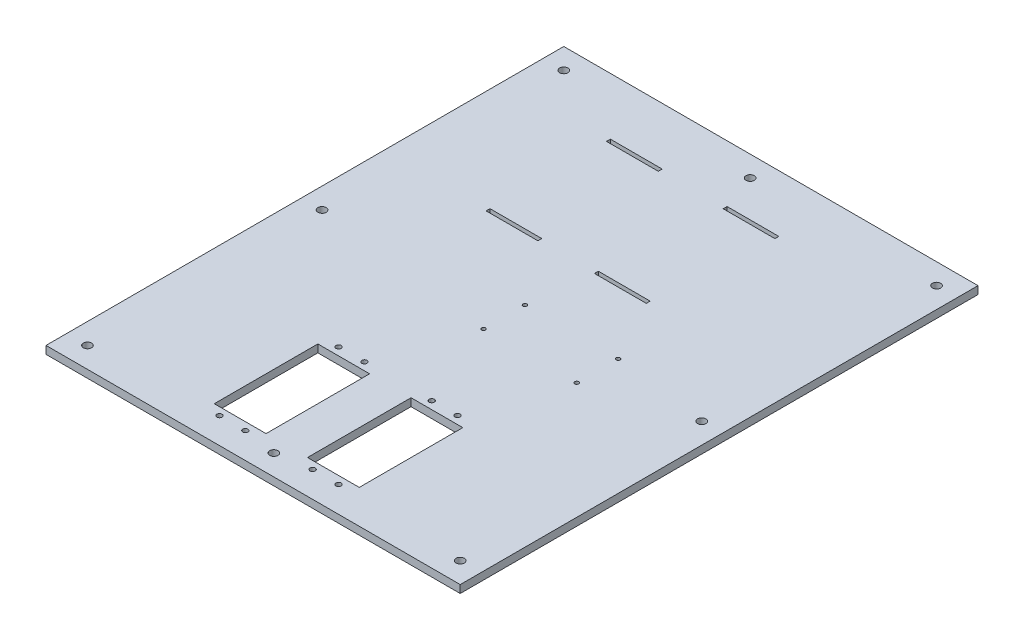
SolidWorks part; units mm, degrees
ref_plane "前视基准面" through (0, 0, 0) normal (0, 0, 1) x (1, 0, 0)
ref_plane "上视基准面" through (0, 0, 0) normal (0, 1, 0) x (1, 0, 0)
ref_plane "右视基准面" through (0, 0, 0) normal (1, 0, 0) x (0, 0, -1)
sketch "草图1" plane through (0, 0, 0) normal (0, 1, 0) x (1, 0, 0)
  line L1 (80, -100) -> (-80, -100)
  line L2 (80, -100) -> (80, 100)
  line L3 (80, 100) -> (-80, 100)
  line L4 (-80, -100) -> (-80, 100)
  line L5 (80, -100) -> (-80, 100) construction
  line L6 (80, 100) -> (-80, -100) construction
  point P0 (0, 0)
  dimension "D1" = 160
  dimension "D2" = 200
extrude "凸台-拉伸2" add sketch "草图1" along normal blind 3
sketch "草图2" plane through (0, 3, 0) normal (0, 1, 0) x (1, 0, 0)
  line L0 (-28, -47) -> (-28, -87)
  line L1 (8, -47) -> (28, -47)
  line L2 (8, -47) -> (8, -87)
  line L3 (8, -87) -> (28, -87)
  line L4 (28, -47) -> (28, -87)
  line L5 (8, -47) -> (28, -87) construction
  line L6 (8, -87) -> (28, -47) construction
  line L7 (-8, -47) -> (-8, -87)
  line L8 (-28, -87) -> (-8, -87)
  line L9 (-28, -47) -> (-8, -87) construction
  line L10 (-28, -87) -> (-8, -47) construction
  line L11 (-28, -47) -> (-8, -47)
  line L12 (-80, -100) -> (80, -100) construction
  circle A0 centre (23, -90) radius 1
  circle A1 centre (13, -44) radius 1
  circle A2 centre (-23, -90) radius 1
  circle A3 centre (-23, -44) radius 1
  circle A4 centre (-13, -44) radius 1
  circle A5 centre (-13, -90) radius 1
  circle A6 centre (13, -90) radius 1
  circle A7 centre (22.9393, -44) radius 1
  point P0 (18, -67)
  point P5 (-18, -67)
  dimension "D9" = 2
  dimension "D8" = 13
  dimension "D10" = 13
  dimension "D7" = 46
  dimension "D14" = 46
  dimension "D15" = 5
  dimension "D16" = 10
  dimension "D17" = 23
  dimension "D3" = 10
  dimension "D18" = 23
  dimension "D19" = 10
  dimension "D21" = 5
  dimension "D13" = 10
  dimension "D1" = 20
  dimension "D2" = 40
  dimension "D4" = 20
  dimension "D5" = 10
  dimension "D6" = 16
  dimension "D11" = 40
  dimension "D12" = 8
  dimension "D20" = 5
  dimension "D22" = 23
  dimension "D23" = 23
extrude "切除-拉伸1" cut sketch "草图2" against normal blind 3
sketch "草图3" plane through (0, 3, 0) normal (0, 1, 0) x (1, 0, 0)
  circle A0 centre (35, -10) radius 0.75
  circle A1 centre (35, 6) radius 0.75
  circle A2 centre (-1, -10) radius 0.75
  circle A3 centre (-1, 6) radius 0.75
  dimension "D1" = 1.5
  dimension "D3" = 35
  dimension "D4" = 16
  dimension "D5" = 16
  dimension "D6" = 10
  dimension "D9" = 36
  dimension "D2" = 35
  dimension "D7" = 10
  dimension "D8" = 36
extrude "切除-拉伸2" cut sketch "草图3" against normal blind 10
sketch "草图4" plane through (0, 3, 0) normal (0, 1, 0) x (1, 0, 0)
  circle A0 centre (72, 1.2844) radius 1.6
  circle A1 centre (-72, -1.3683) radius 1.6
  circle A2 centre (72, 92) radius 1.6
  circle A3 centre (-72, 92) radius 1.6
  circle A4 centre (-72, -92) radius 1.6
  circle A5 centre (72, -92) radius 1.6
  circle A6 centre (0, -92) radius 1.6
  circle A7 centre (0, 92) radius 1.6
  dimension "D5" = 3.2
extrude "切除-拉伸3" cut sketch "草图4" against normal blind 10
sketch "草图5" plane through (0, 3, 0) normal (0, 1, 0) x (1, 0, 0)
  line L1 (-40, 78) -> (-20, 78)
  line L2 (-40, 78) -> (-40, 76.5)
  line L3 (-40, 76.5) -> (-20, 76.5)
  line L4 (-20, 78) -> (-20, 76.5)
  line L5 (-40, 31.5) -> (-20, 31.5)
  line L6 (-40, 31.5) -> (-40, 30)
  line L7 (-40, 30) -> (-20, 30)
  line L8 (-20, 31.5) -> (-20, 30)
  line L9 (5.0688, 76.5) -> (25.0688, 76.5)
  line L10 (5.0688, 76.5) -> (5.0688, 78)
  line L11 (5.0688, 78) -> (25.0688, 78)
  line L12 (25.0688, 76.5) -> (25.0688, 78)
  line L13 (1.8525, 31.5) -> (21.8525, 31.5)
  line L14 (1.8525, 31.5) -> (1.8525, 30)
  line L15 (1.8525, 30) -> (21.8525, 30)
  line L16 (21.8525, 31.5) -> (21.8525, 30)
  dimension "D1" = 20
  dimension "D2" = 20
  dimension "D3" = 20
  dimension "D4" = 20
  dimension "D5" = 1.5
  dimension "D6" = 1.5
  dimension "D7" = 1.5
  dimension "D8" = 1.5
  dimension "D9" = 45
  dimension "D10" = 45
  dimension "D11" = 1.8525
  dimension "D12" = 20
  dimension "D13" = 30
  dimension "D14" = 30
extrude "切除-拉伸4" cut sketch "草图5" against normal blind 10
